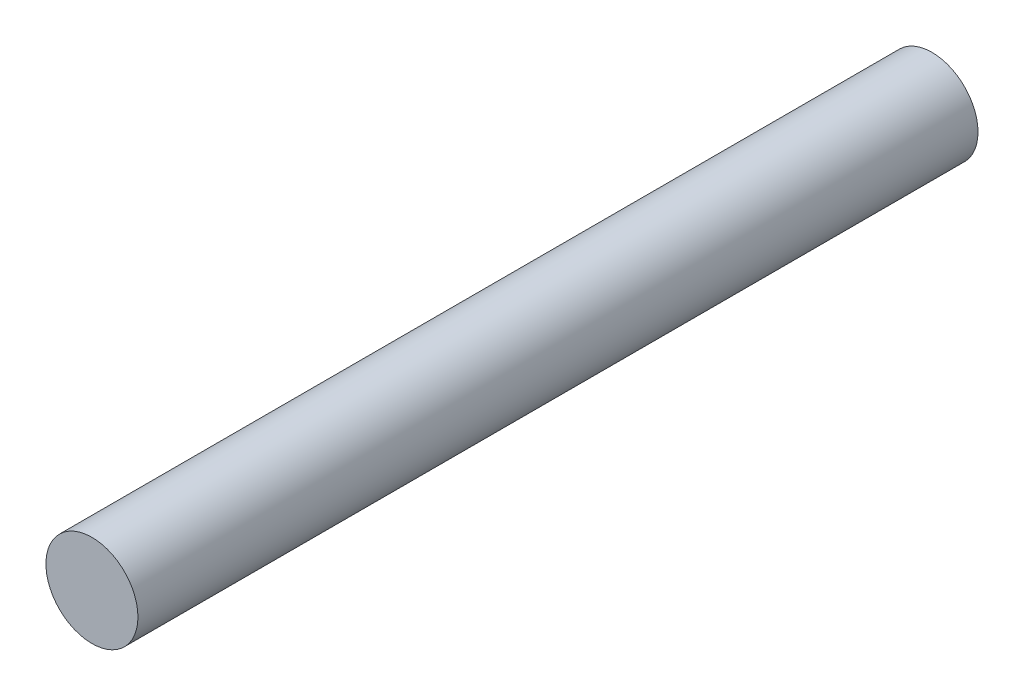
SolidWorks part; units mm, degrees
ref_plane "Front" through (0, 0, 0) normal (0, 0, 1) x (1, 0, 0)
ref_plane "Top" through (0, 0, 0) normal (0, 1, 0) x (1, 0, 0)
ref_plane "Right" through (0, 0, 0) normal (1, 0, 0) x (0, 0, -1)
sketch "Sketch1" plane through (0, 0, 0) normal (0, 0, 1) x (1, 0, 0)
  circle A0 centre (0, 0) radius 3.4925 construction
  circle A1 centre (0, 0) radius 3.4925
extrude "Boss-Extrude1" add sketch "Sketch1" against normal up to surface (63.758 mm away)
